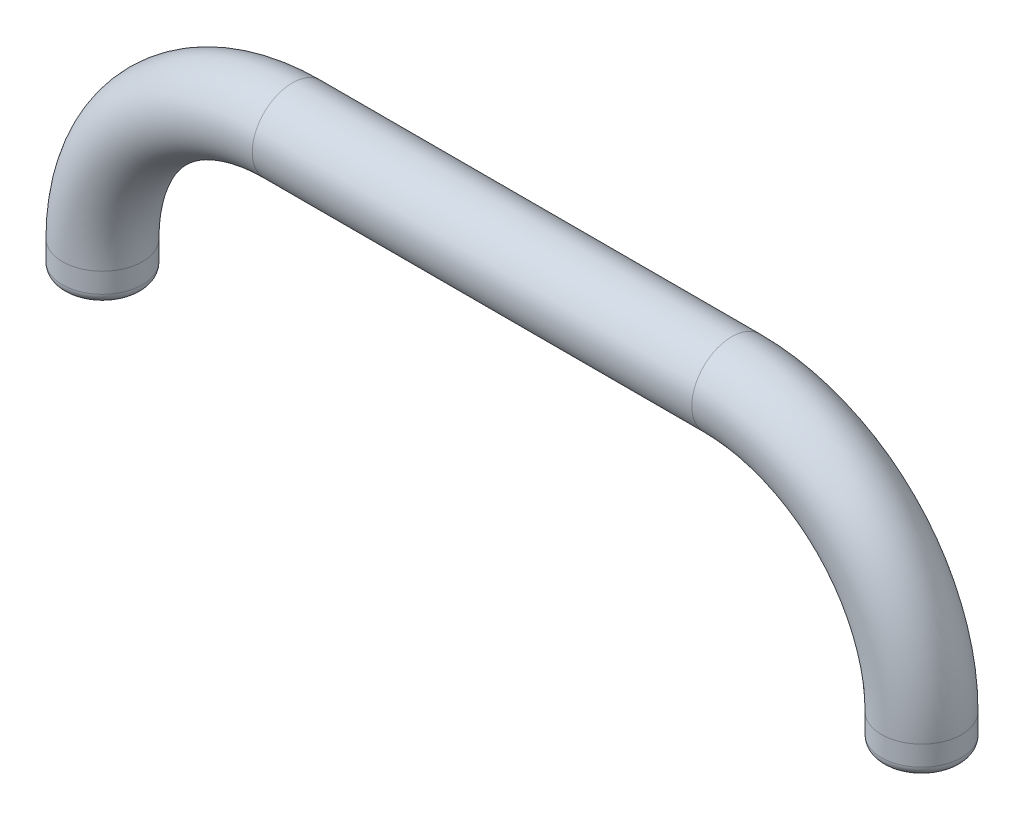
SolidWorks part; units mm, degrees
ref_plane "Plane1" through (0, 0, 0) normal (0, 0, 1) x (1, 0, 0)
ref_plane "Plane2" through (0, 0, 0) normal (0, 1, 0) x (1, 0, 0)
ref_plane "Plane3" through (0, 0, 0) normal (1, 0, 0) x (0, 0, -1)
sketch "Sketch1" plane through (0, 0, 0) normal (0, 0, 1) x (1, 0, 0)
  line L0 (-22, 0) -> (22, 0)
  line L1 (41, -19) -> (41, -22)
  line L2 (0, 0) -> (0, 37.053) construction
  line L3 (-41, -19) -> (-41, -22)
  arc A0 (22, 0) -> (41, -19) centre (22, -19) cw
  arc A1 (-41, -19) -> (-22, 0) centre (-22, -19) cw
  point P9 (41, 0)
  point P12 (-41, 0)
  dimension "D3" = 19
  dimension "D1" = 82
  dimension "D2" = 22
ref_plane "Plane4" through (41, -22, 0) normal (0, -1, 0) x (1, 0, 0)
sketch "Sketch2" plane through (41, -22, 0) normal (0, -1, 0) x (1, 0, 0)
  circle A0 centre (0, 0) radius 4
  dimension "D1" = 8
sweep "Sweep1" add profiles "Sketch2" path "Sketch1"
fillet "Fillet1" radius 1 2 edges at (41, -22, -4) (-41, -22, -4)
